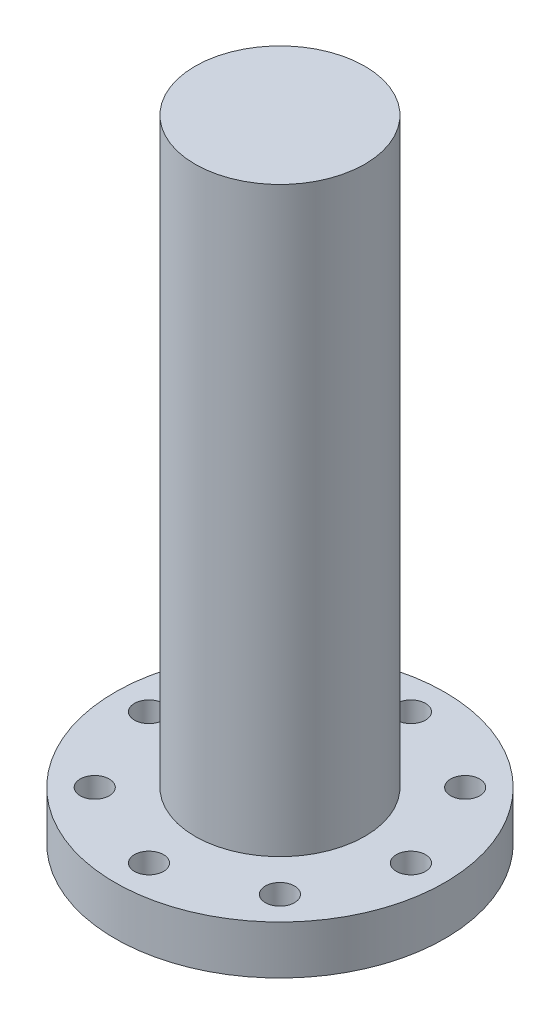
SolidWorks part; units mm, degrees
ref_plane "Front Plane" through (0, 0, 0) normal (0, 0, 1) x (1, 0, 0)
ref_plane "Top Plane" through (0, 0, 0) normal (0, 1, 0) x (1, 0, 0)
ref_plane "Right Plane" through (0, 0, 0) normal (1, 0, 0) x (0, 0, -1)
sketch "Sketch2" plane through (0, 0, 0) normal (1, 0, 0) x (0, 0, -1)
  line L0 (0, 0) -> (0, 46.0228) construction
  line L1 (0, 0) -> (34, 0)
  line L2 (34, 0) -> (34, 10)
  line L3 (34, 10) -> (17.5, 10)
  line L4 (17.5, 10) -> (17.5, 130)
  line L5 (17.5, 130) -> (0, 130)
  line L6 (0, 130) -> (0, 0)
  dimension "D1" = 34
  dimension "D2" = 10
  dimension "D3" = 130
  dimension "D4" = 17.5
revolve "Revolve1" add sketch "Sketch2" angle 360 about L0
sketch "Sketch3" plane through (0, 0, 0) normal (0, -1, 0) x (1, 0, 0)
  circle A0 centre (0, 0) radius 27 construction
  circle A1 centre (0, 27) radius 3
  circle A2 centre (19.0919, 19.0919) radius 3
  circle A3 centre (27, 0) radius 3
  circle A4 centre (19.0919, -19.0919) radius 3
  circle A5 centre (0, -27) radius 3
  circle A6 centre (-19.0919, -19.0919) radius 3
  circle A7 centre (-27, 0) radius 3
  circle A8 centre (-19.0919, 19.0919) radius 3
  dimension "D1" = 54
  dimension "D2" = 6
  dimension "D3" = 8
extrude "Cut-Extrude1" cut sketch "Sketch3" against normal through all contours A3 | A4 | A5 | A6 | A7 | A8 | A1 | A2
